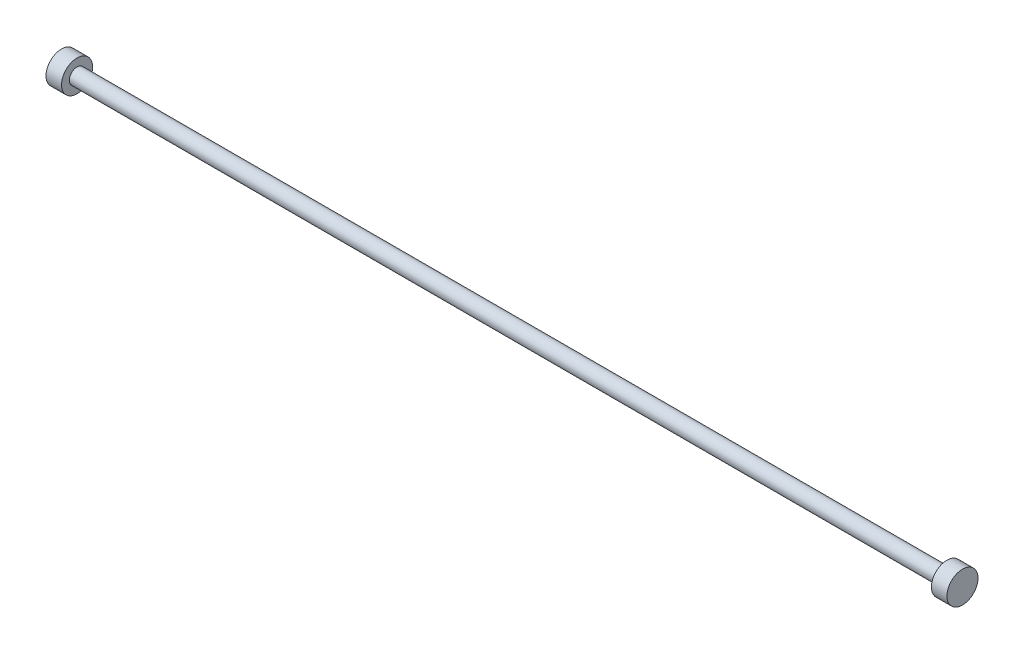
SolidWorks part; units mm, degrees
ref_plane "Front Plane" through (0, 0, 0) normal (0, 0, 1) x (1, 0, 0)
ref_plane "Top Plane" through (0, 0, 0) normal (0, 1, 0) x (1, 0, 0)
ref_plane "Right Plane" through (0, 0, 0) normal (1, 0, 0) x (0, 0, -1)
sketch "Sketch1" plane through (0, 0, 0) normal (1, 0, 0) x (0, 0, -1)
  circle A0 centre (0, 0) radius 5
  dimension "D1" = 10
extrude "Boss-Extrude1" add sketch "Sketch1" along normal blind 560
sketch "Sketch2" plane through (560, 0, 0) normal (1, 0, 0) x (0, 0, -1)
  circle A0 centre (0, 0) radius 10
  dimension "D1" = 20
extrude "Boss-Extrude2" add sketch "Sketch2" along normal blind 10
sketch "Sketch3" plane through (0, 0, 0) normal (-1, 0, 0) x (0, 0, 1)
  circle A0 centre (0, 0) radius 10
  dimension "D1" = 20
extrude "Boss-Extrude3" add sketch "Sketch3" along normal blind 10
